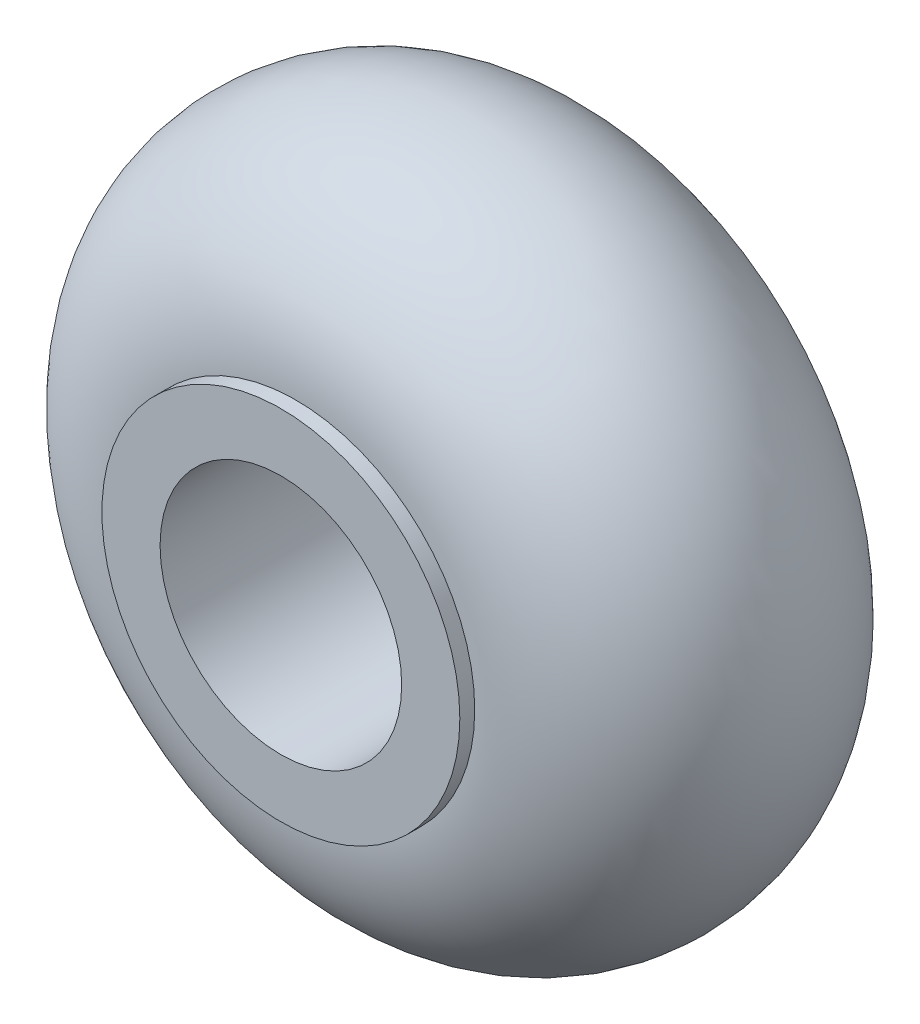
SolidWorks part; units mm, degrees
ref_plane "Front Plane" through (0, 0, 0) normal (0, 0, 1) x (1, 0, 0)
ref_plane "Top Plane" through (0, 0, 0) normal (0, 1, 0) x (1, 0, 0)
ref_plane "Right Plane" through (0, 0, 0) normal (1, 0, 0) x (0, 0, -1)
sketch "Sketch1" plane through (0, 0, 0) normal (1, 0, 0) x (0, 0, -1)
  line L0 (-10.3654, 0) -> (12.6923, 0) construction
  line L2 (0, 0) -> (0, 15.0721) construction
  line L3 (-5.5, 6) -> (-6, 6)
  line L4 (-6, 6) -> (-6, 4.05)
  line L5 (-6, 4.05) -> (6, 4.05)
  line L6 (6, 4.05) -> (6, 6)
  line L7 (6, 6) -> (5.5, 6)
  arc A0 (5.5, 6) -> (-5.5, 6) centre (0, 6.0817) ccw
  dimension "D3" = 5.5006
  dimension "D1" = 11
  dimension "D2" = 6
  dimension "D4" = 0.5
  dimension "D5" = 0.5
  dimension "D6" = 4.05
  dimension "D7" = 5.5
  dimension "D8" = 6
  dimension "D9" = 6
revolve "Revolve1" add sketch "Sketch1" angle 360 about L0
